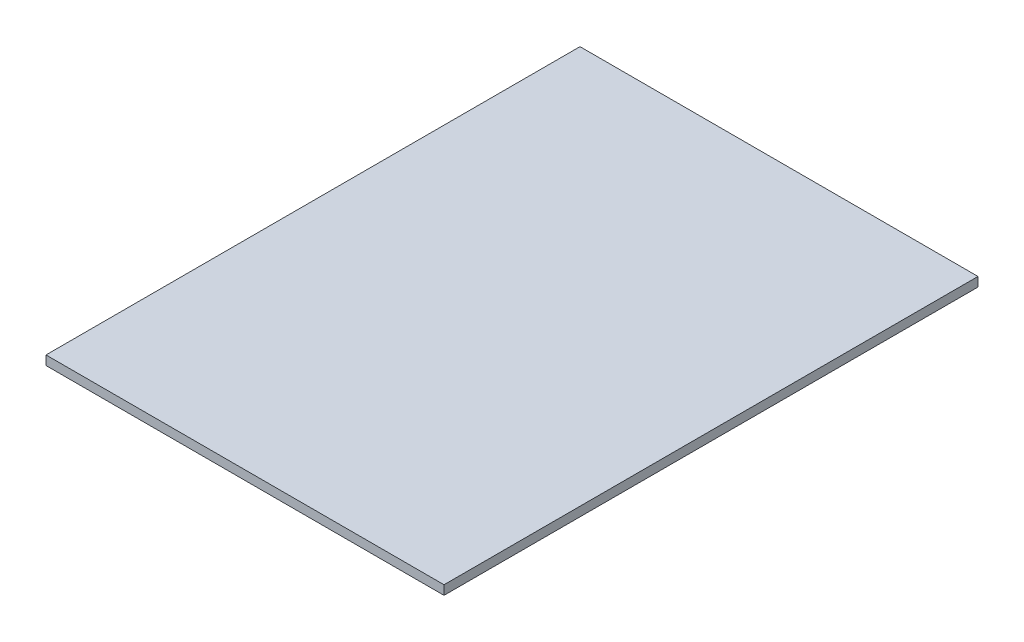
SolidWorks part; units mm, degrees
material "Acrylic (Medium-high impact)"
ref_plane "Front Plane" through (0, 0, 0) normal (0, 0, 1) x (1, 0, 0)
ref_plane "Top Plane" through (0, 0, 0) normal (0, 1, 0) x (1, 0, 0)
ref_plane "Right Plane" through (0, 0, 0) normal (1, 0, 0) x (0, 0, -1)
sketch "Sketch1" plane through (0, 0, 0) normal (0, 1, 0) x (1, 0, 0)
  line L1 (0, 0) -> (87.828, 0)
  line L2 (0, 0) -> (0, 117.828)
  line L3 (0, 117.828) -> (87.828, 117.828)
  line L4 (87.828, 0) -> (87.828, 117.828)
  dimension "D1" = 117.828
  dimension "D2" = 87.828
extrude "Boss-Extrude1" add sketch "Sketch1" along normal blind 2.032
